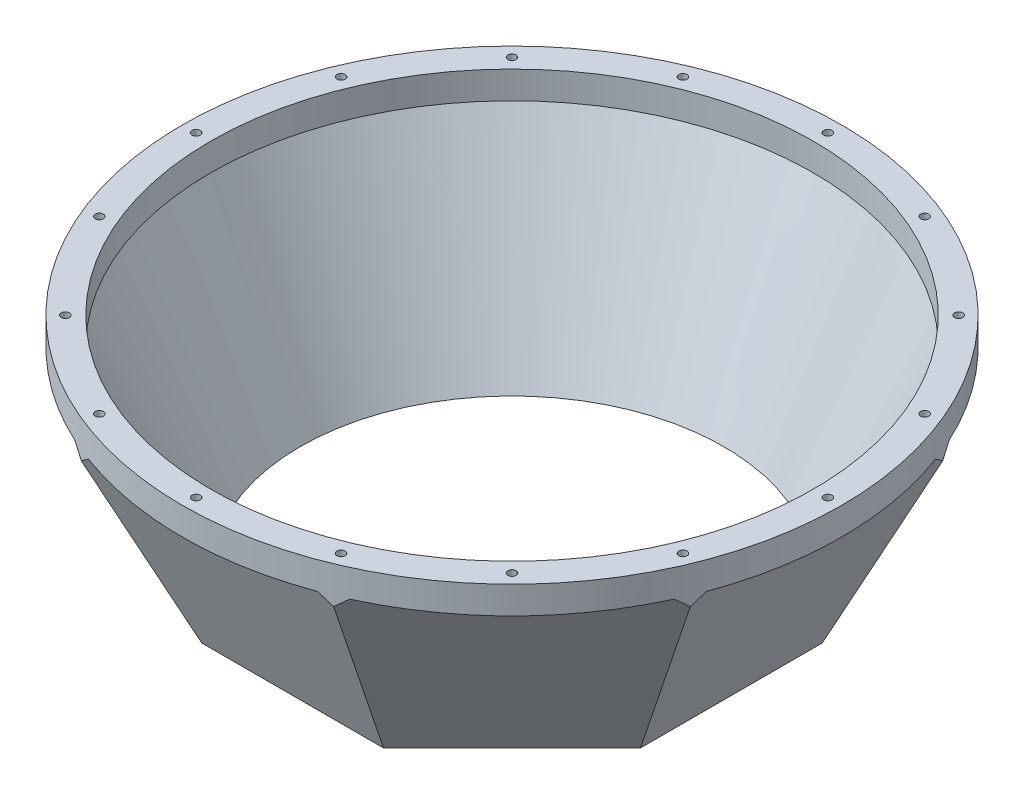
SolidWorks part; units mm, degrees
material "6061-T6 (SS)"
ref_plane "Front Plane" through (0, 0, 0) normal (0, 0, 1) x (1, 0, 0)
ref_plane "Top Plane" through (0, 0, 0) normal (0, 1, 0) x (1, 0, 0)
ref_plane "Right Plane" through (0, 0, 0) normal (1, 0, 0) x (0, 0, -1)
sketch "Sketch3" plane through (0, 0, 0) normal (0, 1, 0) x (1, 0, 0)
  circle A0 centre (0, 0) radius 152.4
  dimension "D1" = 304.8
extrude "Boss-Extrude1" add sketch "Sketch3" along normal blind 101.6
sketch "Sketch4" plane through (0, 0, 0) normal (0, 0, 1) x (1, 0, 0)
  line L0 (142.875, 88.9) -> (101.4202, 0)
  line L2 (101.4202, 0) -> (152.4, 0)
  line L3 (142.875, 88.9) -> (152.4, 88.9)
  line L6 (152.4, 0) -> (152.4, 101.6) construction
  line L7 (152.4, 88.9) -> (152.4, 0)
  line L8 (152.4, 101.6) -> (-152.4, 101.6) construction
  dimension "D1" = 25
  dimension "D2" = 12.7
  dimension "D3" = 9.525
extrude "Cut-Extrude1" cut sketch "Sketch4" against normal through all both and the other way through all
pattern_circular "CirPattern1" count 8 over 360 about axis through (0, 0, 0) along (0, 1, 0) of "Cut-Extrude1"
sketch "Sketch7" plane through (0, 0, 0) normal (0, 0, 1) x (1, 0, 0)
  line L0 (97.917, 0) -> (139.3718, 88.9)
  line L1 (139.3718, 88.9) -> (139.3718, 101.6)
  line L2 (139.3718, 101.6) -> (0, 101.6)
  line L3 (0, 101.6) -> (0, 0)
  line L4 (0, 0) -> (97.917, 0)
  line L5 (140.7992, 84.4485) -> (101.4202, 0) construction
  line L6 (63.5279, 88.9) -> (138.5278, 88.9) construction
  line L7 (152.4, 101.6) -> (-152.4, 101.6) construction
  dimension "D1" = 3.175
revolve "Cut-Revolve1" cut sketch "Sketch7" angle 360 about L3
hole_wizard "#10-24 Tapped Hole1" positions "Sketch8" profile "Sketch9" tap size "#10-24" standard "ANSI Inch"
sketch "Sketch8" plane through (0, 101.6, 0) normal (0, 1, 0) x (1, 0, 0)
  line L0 (146.05, 0) -> (0, 0)
  point P0 (146.05, 0)
  dimension "D1" = 146.05
sketch "Sketch9" plane through (146.05, 101.6, 0) normal (1, 0, 0) x (0, 0, 1)
  line L0 (0, 0) -> (0, 14.0948)
  line L1 (0, 14.0948) -> (1.8986, 12.954)
  line L2 (1.8986, 12.954) -> (1.8986, 0)
  line L5 (1.8986, 0) -> (0, 0)
  line L10 (0, 14.0948) -> (-1.8987, 12.954) construction
  line L11 (0, -6.35) -> (0, 107.95) construction
  dimension "Tap Drill Dia." = 3.7973
  dimension "Tap Drill Depth" = 12.954
  dimension "Drill Angle" = 118
cosmetic thread "Hole Thread1" parameters "D1"=9.652, "D2"=4.826
pattern_circular "CirPattern2" count 16 over 360 about axis through (0, 0, 0) along (0, 1, 0) of "#10-24 Tapped Hole1"
